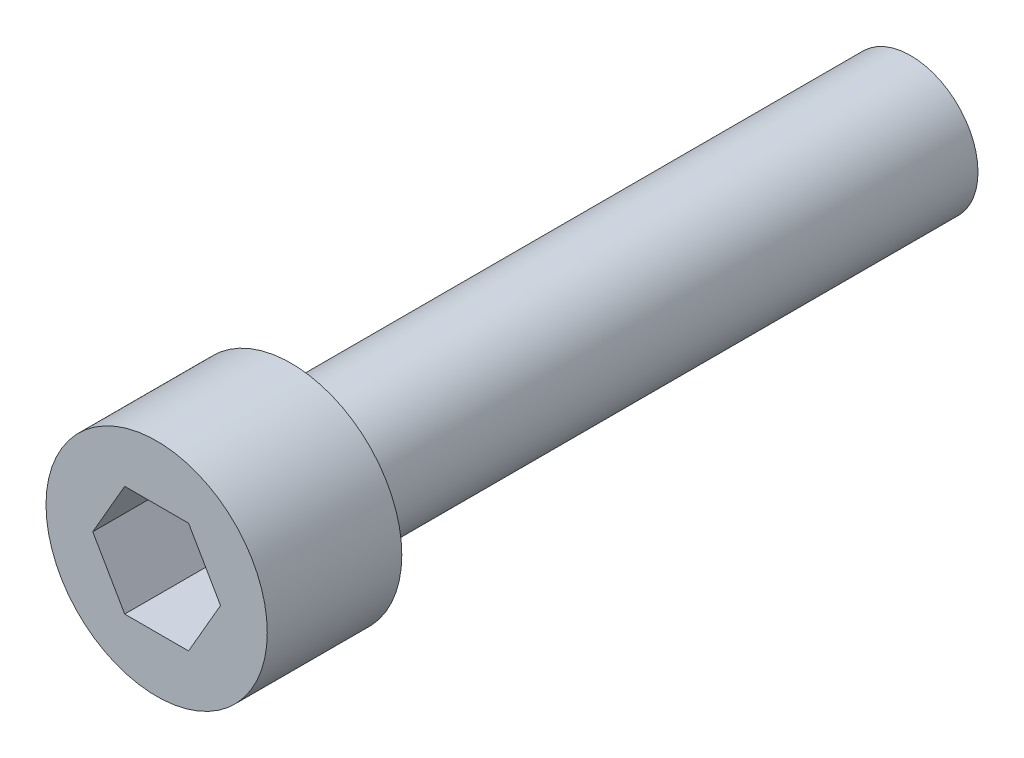
SolidWorks part; units mm, degrees
material "Cast Alloy Steel"
ref_plane "Front Plane" through (0, 0, 0) normal (0, 0, 1) x (1, 0, 0)
ref_plane "Top Plane" through (0, 0, 0) normal (0, 1, 0) x (1, 0, 0)
ref_plane "Right Plane" through (0, 0, 0) normal (1, 0, 0) x (0, 0, -1)
sketch "Sketch1" plane through (0, 0, 0) normal (0, 0, 1) x (1, 0, 0)
  circle A0 centre (0, 0) radius 2.413
  dimension "D1" = 4.826
extrude "Boss-Extrude1" add sketch "Sketch1" along normal blind 22.225
sketch "Sketch2" plane through (0, 0, 22.225) normal (0, 0, 1) x (1, 0, 0)
  circle A0 centre (0, 0) radius 3.9688
  dimension "D1" = 7.9375
extrude "Boss-Extrude2" add sketch "Sketch2" along normal blind 4.826
sketch "Sketch3" plane through (0, 0, 27.051) normal (0, 0, 1) x (1, 0, 0)
  line L1 (2.2914, 0) -> (1.1457, 1.9844)
  line L2 (1.1457, 1.9844) -> (-1.1457, 1.9844)
  line L3 (-1.1457, 1.9844) -> (-2.2914, 0)
  line L4 (-2.2914, 0) -> (-1.1457, -1.9844)
  line L5 (-1.1457, -1.9844) -> (1.1457, -1.9844)
  line L6 (1.1457, -1.9844) -> (2.2914, 0)
  circle A0 centre (0, 0) radius 1.9844 construction
  dimension "D1" = 3.9688
extrude "Cut-Extrude1" cut sketch "Sketch3" against normal blind 3.81
